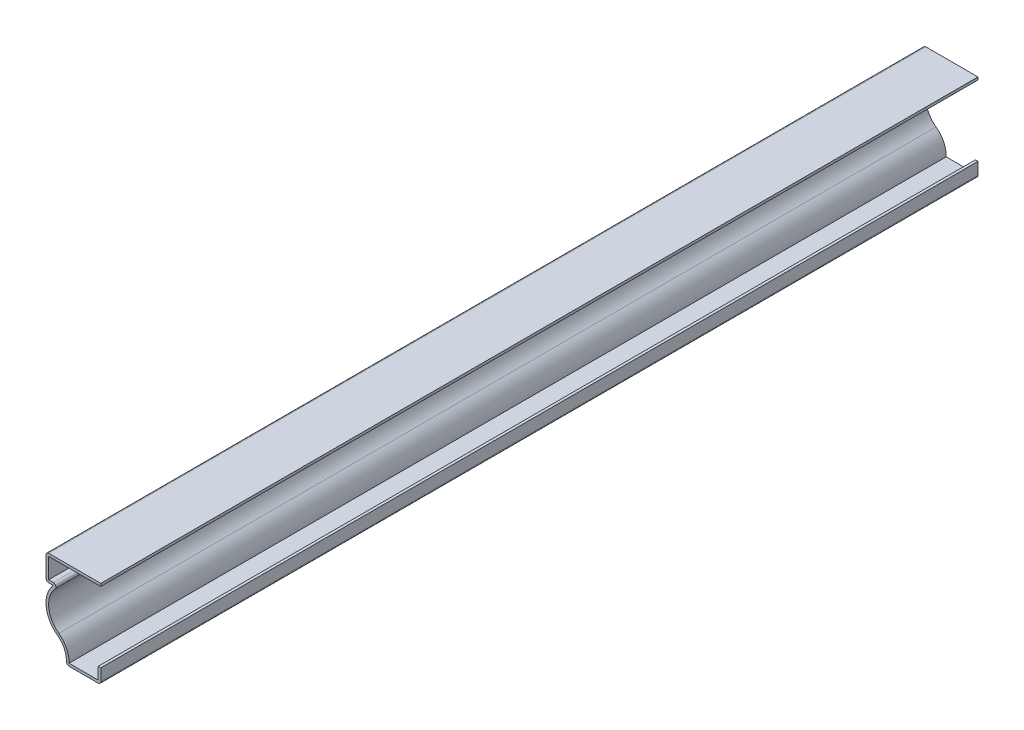
SolidWorks part; units mm, degrees
ref_plane "Front Plane" through (0, 0, 0) normal (0, 0, 1) x (1, 0, 0)
ref_plane "Top Plane" through (0, 0, 0) normal (0, 1, 0) x (1, 0, 0)
ref_plane "Right Plane" through (0, 0, 0) normal (1, 0, 0) x (0, 0, -1)
sketch "Sketch1" plane through (0, 0, 0) normal (0, 0, 1) x (1, 0, 0)
  line L0 (0, 6.35) -> (0, 0)
  line L1 (0, 0) -> (-15.0812, 0)
  line L2 (-20.6375, 26.9875) -> (-23.8125, 26.9875)
  line L3 (-23.8125, 26.9875) -> (-23.8125, 38.1)
  line L4 (-23.8125, 38.1) -> (0, 38.1)
  line L5 (-23.8125, 26.9875) -> (-23.8125, 0) construction
  arc A0 (-15.0812, 0) -> (-18.8923, 9.2516) centre (-24.4812, 1.5386) ccw
  arc A1 (-18.8923, 9.2516) -> (-20.6375, 26.9875) centre (-11.9062, 18.8928) cw
  point P31 (-11.9063, 38.1)
  dimension "D7" = 9.525
  dimension "D1" = 23.8125
  dimension "D2" = 6.35
  dimension "D3" = 38.1
  dimension "D4" = 11.1125
  dimension "D5" = 15.0812
  dimension "D6" = 3.175
extrude "Extrude-Thin1" add sketch "Sketch1" against normal blind 381 thin
fillet "Fillet1" radius 1.143 5 edges at (0, 0, -190.5) (-15.0812, 0, -190.5) (-17.4301, 28.1305, -190.5) (-23.8125, 26.9875, -190.5) (-23.8125, 38.1, -190.5)
